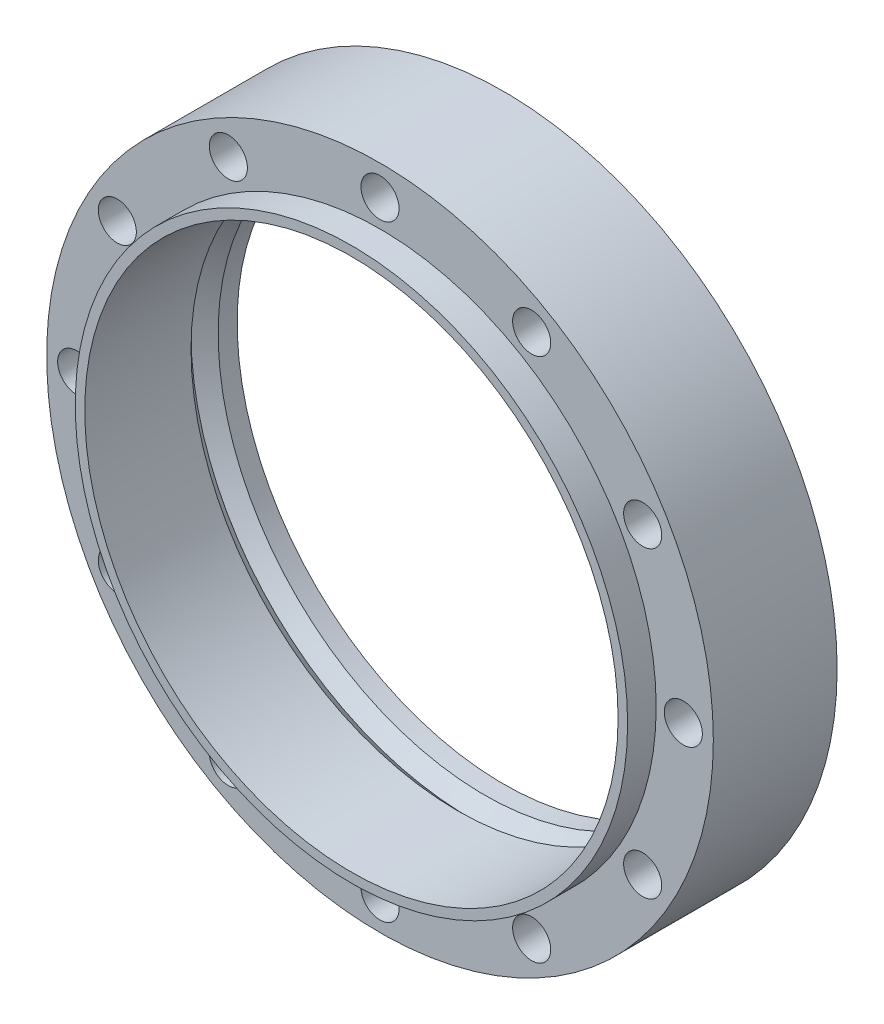
SolidWorks part; units mm, degrees
ref_plane "前视基准面" through (0, 0, 0) normal (0, 0, 1) x (1, 0, 0)
ref_plane "上视基准面" through (0, 0, 0) normal (0, 1, 0) x (1, 0, 0)
ref_plane "右视基准面" through (0, 0, 0) normal (1, 0, 0) x (0, 0, -1)
sketch "草图1" plane through (0, 0, 0) normal (0, 0, 1) x (1, 0, 0)
  circle A0 centre (0, 0) radius 35
extrude "凸台-拉伸1" add sketch "草图1" along normal blind 16
sketch "草图2" plane through (0, 0, 16) normal (0, 0, 1) x (1, 0, 0)
  circle A0 centre (0, 0) radius 29
  circle A1 centre (0, 0) radius 35
extrude "切除-拉伸1" cut sketch "草图2" against normal blind 3
sketch "草图3" plane through (0, 0, 16) normal (0, 0, 1) x (1, 0, 0)
  circle A0 centre (0, 0) radius 28
extrude "切除-拉伸2" cut sketch "草图3" against normal through all
sketch "草图4" plane through (0, 0, 13) normal (0, 0, 1) x (1, 0, 0)
  circle A0 centre (0, 31.8479) radius 2
extrude "切除-拉伸3" cut sketch "草图4" against normal through all
pattern_circular "阵列(圆周)1" count 12 over 360 about axis through (0, 0, 0) along (0, 0, 1) of "切除-拉伸3"
ref_plane "基准面1" through (0, 0, 6) normal (0, 0, 1) x (1, 0, 0)
sketch "草图5" plane through (0, 0, 0) normal (1, 0, 0) x (0, 0, -1)
  line L0 (0, 0) -> (-9.4309, 0)
  line L3 (-4.8554, 27.9882) -> (-1.9828, 27.9865)
  line L4 (-1.9828, 27.9865) -> (-3.4199, 29.4236)
  line L5 (-3.4199, 29.4236) -> (-4.8554, 27.9882)
revolve "切除-旋转3" cut sketch "草图5" angle 360 about L0
